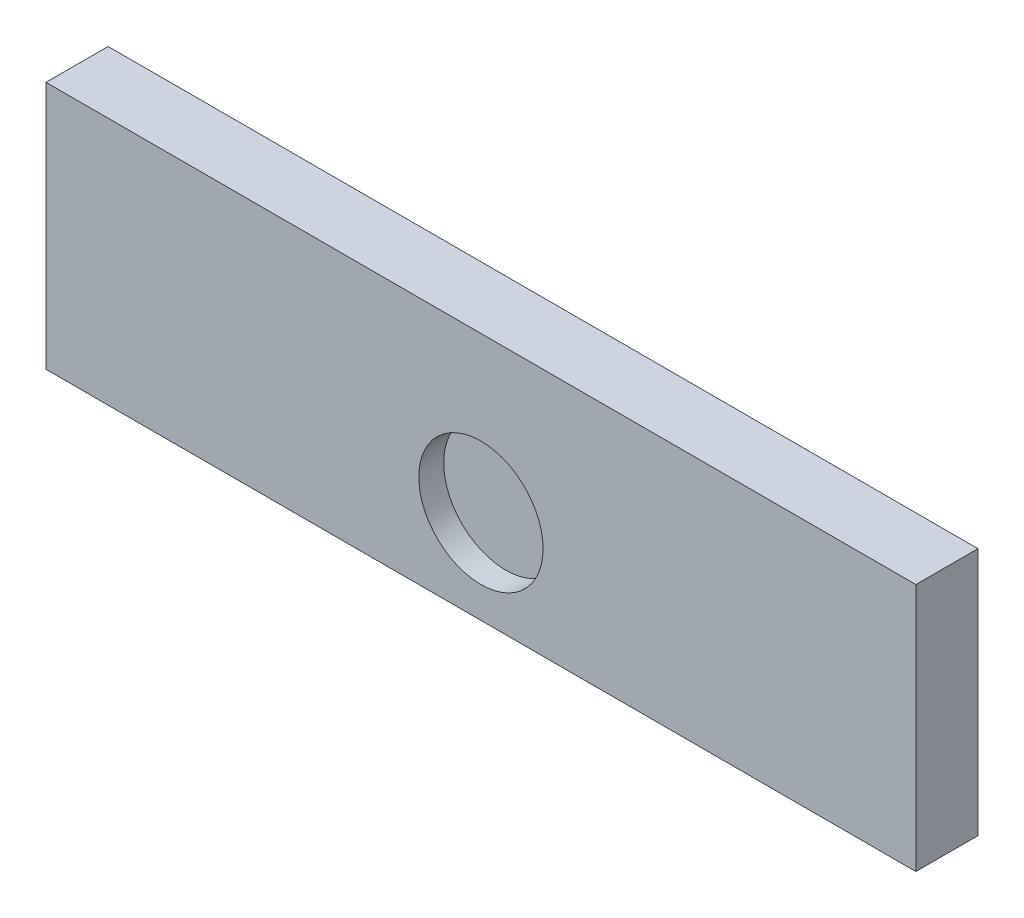
SolidWorks part; units mm, degrees
ref_plane "Front Plane" through (0, 0, 0) normal (0, 0, 1) x (1, 0, 0)
ref_plane "Top Plane" through (0, 0, 0) normal (0, 1, 0) x (1, 0, 0)
ref_plane "Right Plane" through (0, 0, 0) normal (1, 0, 0) x (0, 0, -1)
sketch "Sketch1" plane through (0, 0, 0) normal (0, 0, 1) x (1, 0, 0)
  line L1 (-70, 20) -> (70, 20)
  line L2 (-70, 20) -> (-70, -20)
  line L3 (-70, -20) -> (70, -20)
  line L4 (70, 20) -> (70, -20)
  line L5 (-70, 20) -> (70, -20) construction
  line L6 (-70, -20) -> (70, 20) construction
  point P0 (0, 0)
  dimension "D1" = 140
  dimension "D2" = 40
extrude "Boss-Extrude1" add sketch "Sketch1" along normal blind 10
sketch "Sketch3" plane through (0, 0, 10) normal (0, 0, 1) x (1, 0, 0)
  line L0 (-70, -20) -> (70, -20) construction
  circle A0 centre (0, -5) radius 10
  dimension "D1" = 20
  dimension "D2" = 15
extrude "Cut-Extrude2" cut sketch "Sketch3" against normal blind 4
